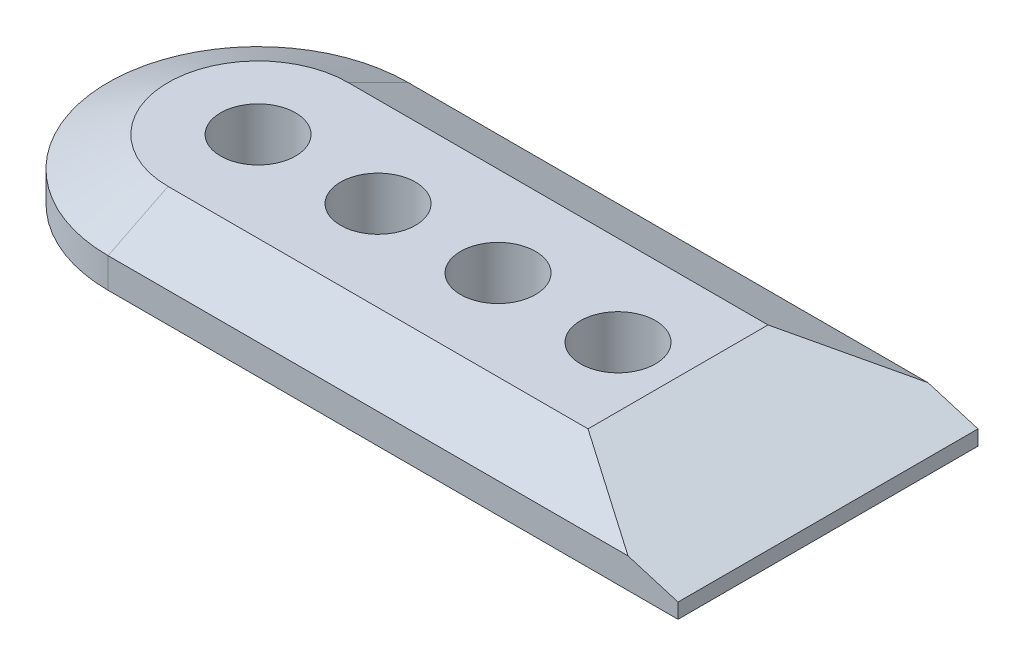
SolidWorks part; units mm, degrees
ref_plane "Front Plane" through (0, 0, 0) normal (0, 0, 1) x (1, 0, 0)
ref_plane "Top Plane" through (0, 0, 0) normal (0, 1, 0) x (1, 0, 0)
ref_plane "Right Plane" through (0, 0, 0) normal (1, 0, 0) x (0, 0, -1)
sketch "Sketch13" plane through (0, 0, 0) normal (0, 1, 0) x (1, 0, 0)
  line L0 (0, 31.75) -> (120.65, 31.75)
  line L1 (120.65, -31.75) -> (120.65, 31.75)
  line L2 (0, -31.75) -> (120.65, -31.75)
  arc A0 (0, 31.75) -> (0, -31.75) centre (0, 0) ccw
  dimension "D1" = 31.75
  dimension "D2" = 120.65
  dimension "D3" = 63.5
extrude "Boss-Extrude2" add sketch "Sketch13" along normal blind 12.7
chamfer "Chamfer3" distance 6.35 distance2 12.7 3 edges at (60.325, 12.7, -31.75) (-31.75, 12.7, 0) (60.325, 12.7, 31.75)
chamfer "Chamfer4" distance 9.525 distance2 31.75 1 edges at (120.65, 12.7, 0)
sketch "Sketch14" plane through (0, 12.7, 0) normal (0, 1, 0) x (1, 0, 0)
  circle A0 centre (0, 0) radius 7.9375
  circle A5 centre (25.4, 0) radius 7.9375
  circle A6 centre (50.8, 0) radius 7.9375
  circle A7 centre (76.2, 0) radius 7.9375
  dimension "D1" = 15.875
  dimension "D3" = 25.4
  dimension "D2" = 4
extrude "Cut-Extrude3" cut sketch "Sketch14" against normal through all contours A0 | A5 | A7 | A6
